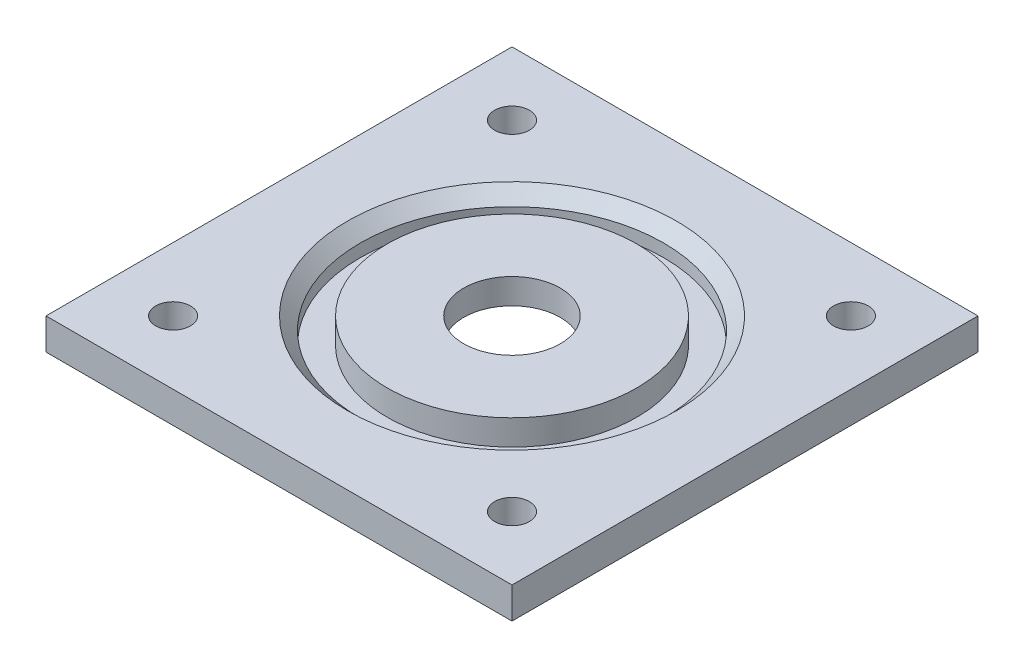
SolidWorks part; units mm, degrees
ref_plane "Front Plane" through (0, 0, 0) normal (0, 0, 1) x (1, 0, 0)
ref_plane "Top Plane" through (0, 0, 0) normal (0, 1, 0) x (1, 0, 0)
ref_plane "Right Plane" through (0, 0, 0) normal (1, 0, 0) x (0, 0, -1)
sketch "Sketch1" plane through (0, 0, 0) normal (0, 0, 1) x (1, 0, 0)
  line L0 (0, 0) -> (5.8, 0)
  line L1 (5.8, 0) -> (5.8, -0.7)
  line L2 (5.8, -0.7) -> (19.7672, -0.7)
  line L3 (19.7672, -0.7) -> (19.7672, 0)
  line L4 (19.7672, 0) -> (9.03, 0)
  line L5 (9.03, 0) -> (9.03, 3)
  line L6 (9.03, 3) -> (0, 3)
  line L7 (0, 3) -> (0, 0)
  line L8 (-5.7, -3.5493) -> (-5.7, 12.6338) construction
  line L9 (-11.4, 3) -> (-11.4, 0)
  line L10 (-20.43, 3) -> (-11.4, 3)
  line L11 (-20.43, 0) -> (-20.43, 3)
  line L12 (-31.1672, 0) -> (-20.43, 0)
  line L13 (-31.1672, -0.7) -> (-31.1672, 0)
  line L14 (-17.2, -0.7) -> (-31.1672, -0.7)
  line L15 (-17.2, 0) -> (-17.2, -0.7)
  line L16 (-11.4, 0) -> (-17.2, 0)
  dimension "D1" = 3
  dimension "D2" = 11.4
  dimension "D3" = 9.03
  dimension "D4" = 0.7
  dimension "D5" = 23
  dimension "D6" = 3
revolve "Revolve1" add sketch "Sketch1" angle 360 about L8
sketch "Sketch2" plane through (0, 0, 0) normal (0, 1, 0) x (1, 0, 0)
  line L5 (-33.2, -27.5) -> (21.8, 27.5) construction
  line L6 (-33.2, 27.5) -> (21.8, -27.5) construction
  line L7 (-33.2, 27.5) -> (21.8, 27.5)
  line L8 (-33.2, 27.5) -> (-33.2, -27.5)
  line L9 (-33.2, -27.5) -> (21.8, -27.5)
  line L10 (21.8, 27.5) -> (21.8, -27.5)
  circle A0 centre (-5.7, 0) radius 17.1
  circle A2 centre (-5.7, 0) radius 5.7 construction
  point P3 (24.1355, 29.8355)
  dimension "D1" = 11.4
  dimension "D2" = 55
  dimension "D3" = 55
extrude "Boss-Extrude1" add sketch "Sketch2" against normal up to surface (0.7 mm away) up to face at (-5.7, -0.7, -25.4672)
sketch "Sketch3" plane through (0, 0, 0) normal (0, 1, 0) x (1, 0, 0)
  line L5 (-33.2, -27.5) -> (21.8, -27.5)
  line L6 (-33.2, -27.5) -> (-33.2, 27.5)
  line L7 (-33.2, 27.5) -> (21.8, 27.5)
  line L8 (21.8, -27.5) -> (21.8, 27.5)
  line L9 (-33.2, -27.5) -> (21.8, 27.5) construction
  line L10 (-33.2, 27.5) -> (21.8, -27.5) construction
  circle A0 centre (-5.7, 0) radius 17.905
  circle A1 centre (-5.7, 0) radius 14.73 construction
  dimension "D1" = 3.175
  dimension "D2" = 55
extrude "Boss-Extrude2" add sketch "Sketch3" along normal up to surface (3 mm away) up to face at (-5.7, 3, -5.7)
sketch "Sketch5" plane through (0, 3, 0) normal (0, 1, 0) x (1, 0, 0)
  line L1 (-25.7, -20) -> (14.3, -20) construction
  line L2 (-25.7, -20) -> (-25.7, 20) construction
  line L3 (-25.7, 20) -> (14.3, 20) construction
  line L4 (14.3, -20) -> (14.3, 20) construction
  line L5 (-25.7, -20) -> (14.3, 20) construction
  line L6 (-25.7, 20) -> (14.3, -20) construction
  circle A0 centre (14.3, 20) radius 2.05
  circle A1 centre (-25.7, 20) radius 2.05
  circle A2 centre (-25.7, -20) radius 2.05
  circle A3 centre (14.3, -20) radius 2.05
  point P0 (-5.7, 0)
  dimension "D1" = 4.1
  dimension "D2" = 40
extrude "Cut-Extrude1" cut sketch "Sketch5" against normal blind 10
chamfer "Chamfer1" distance 1.5 angle 45 1 edges at (-5.7, 3, 17.905)
